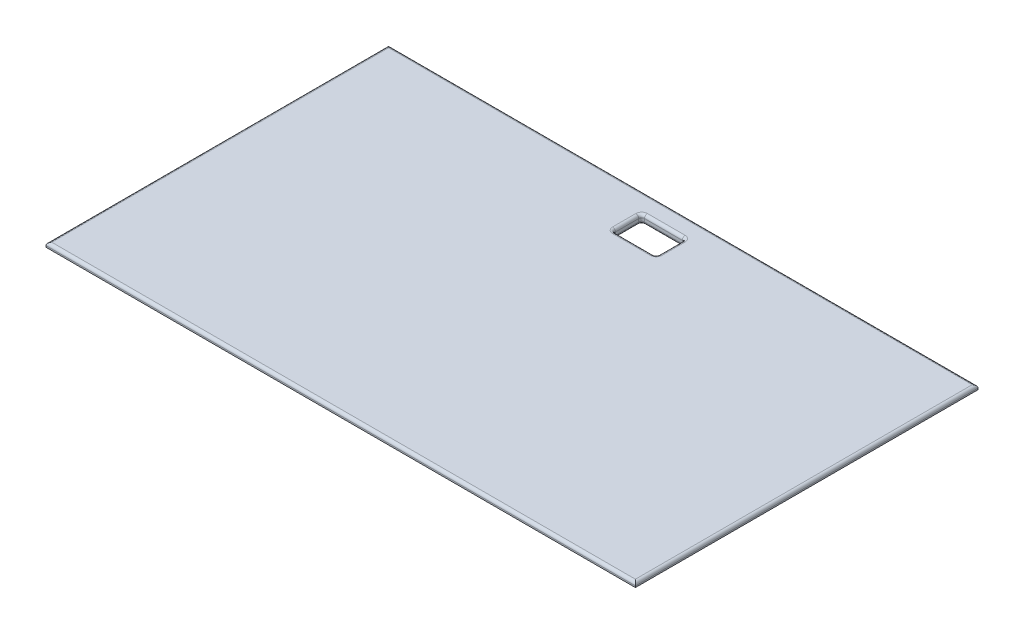
SolidWorks part; units mm, degrees
ref_plane "前视基准面" through (0, 0, 0) normal (0, 0, 1) x (1, 0, 0)
ref_plane "上视基准面" through (0, 0, 0) normal (0, 1, 0) x (1, 0, 0)
ref_plane "右视基准面" through (0, 0, 0) normal (1, 0, 0) x (0, 0, -1)
other "Configuration Table"
sketch "草图1" plane through (0, 0, 0) normal (0, 1, 0) x (1, 0, 0)
  line L1 (-100, -57.5) -> (100, -57.5)
  line L2 (-100, -57.5) -> (-100, 57.5)
  line L3 (-100, 57.5) -> (100, 57.5)
  line L4 (100, -57.5) -> (100, 57.5)
  line L5 (-100, -57.5) -> (100, 57.5) construction
  line L6 (-100, 57.5) -> (100, -57.5) construction
  point P0 (0, 0)
  dimension "D1" = 115
  dimension "D2" = 200
extrude "凸台-拉伸1" add sketch "草图1" along normal blind 1.5
ref_plane "基准面1" through (0, 1.5, 0) normal (0, 1, 0) x (1, 0, 0)
sketch "草图2" plane through (0, 1.5, 0) normal (0, 1, 0) x (1, 0, 0)
  line L0 (100, -57.5) -> (100, 57.5) construction
  line L1 (100, 57.5) -> (-100, 57.5) construction
  line L2 (100, -57.5) -> (100, 57.5) construction
  line L3 (100, 57.5) -> (-100, 57.5) construction
  line L21 (-101.5, -59) -> (101.5, -59)
  line L22 (-101.5, -59) -> (-101.5, 59)
  line L23 (-101.5, 59) -> (101.5, 59)
  line L24 (101.5, -59) -> (101.5, 59)
  line L25 (-101.5, -59) -> (101.5, 59) construction
  line L26 (-101.5, 59) -> (101.5, -59) construction
  point P2 (0, 0)
  dimension "D1" = 1.5
  dimension "D2" = 1.5
extrude "凸台-拉伸2" add sketch "草图2" along normal blind 1.5
sketch "草图3" plane through (0, 0, 0) normal (0, -1, 0) x (1, 0, 0)
  line L0 (0, 0) -> (0, -57.5) construction
  line L1 (100, -57.5) -> (-100, -57.5) construction
  line L3 (-7.5, -42.148) -> (7.5, -42.148)
  line L4 (-7.5, -42.148) -> (-7.5, -52.148)
  line L5 (-7.5, -52.148) -> (7.5, -52.148)
  line L6 (7.5, -42.148) -> (7.5, -52.148)
  line L7 (-7.5, -42.148) -> (7.5, -52.148) construction
  line L8 (-7.5, -52.148) -> (7.5, -42.148) construction
  point P5 (0, -47.148)
  dimension "D1" = 10
  dimension "D2" = 15
extrude "切除-拉伸1" cut sketch "草图3" against normal blind 11.5
fillet "圆角2" radius 1 12 edges at (7.5, 0, -47.148) (0, 0, -52.148) (0, 0, -42.148) (-7.5, 0, -47.148) (0, 3, -52.148) (7.5, 3, -47.148) (0, 3, -42.148) (-7.5, 3, -47.148) (-7.5, 1.5, -52.148) (7.5, 1.5, -52.148) (-7.5, 1.5, -42.148) (7.5, 1.5, -42.148)
fillet "圆角3" radius 1 4 edges at (0, 3, 59) (-101.5, 3, 0) (0, 3, -59) (101.5, 3, 0)
sketch "草图4" plane through (0, 0, 0) normal (0, -1, 0) x (1, 0, 0)
  line L0 (0, 57.5) -> (0, -57.5) construction
  line L1 (-100, 57.5) -> (100, 57.5) construction
  line L2 (100, -57.5) -> (-100, -57.5) construction
  line L3 (-100, 29.0019) -> (100, 29.0019) construction
  line L4 (26.25, -1.494) -> (-26.25, -1.494) construction
  line L5 (26.25, -1.494) -> (26.25, -30.294) construction
  line L6 (26.25, -30.294) -> (-26.25, -30.294) construction
  line L7 (-26.25, -1.494) -> (-26.25, -30.294) construction
  line L8 (26.25, -1.494) -> (-26.25, -30.294) construction
  line L9 (26.25, -30.294) -> (-26.25, -1.494) construction
  line L10 (-100, -57.5) -> (-100, 57.5) construction
  line L11 (100, 57.5) -> (100, -57.5) construction
  line L12 (-64.6953, 41.0019) -> (-64.6953, 42.5019)
  line L13 (-27.1953, 17.0019) -> (-69.6953, 17.0019) construction
  line L14 (-27.1953, 17.0019) -> (-27.1953, 41.0019) construction
  line L15 (-27.1953, 41.0019) -> (-69.6953, 41.0019) construction
  line L16 (-69.6953, 17.0019) -> (-69.6953, 41.0019) construction
  line L17 (-27.1953, 17.0019) -> (-69.6953, 41.0019) construction
  line L18 (-27.1953, 41.0019) -> (-69.6953, 17.0019) construction
  line L19 (25.3357, 14.2519) -> (78.8357, 14.2519) construction
  line L20 (25.3357, 14.2519) -> (25.3357, 43.7519) construction
  line L21 (25.3357, 43.7519) -> (78.8357, 43.7519) construction
  line L22 (78.8357, 14.2519) -> (78.8357, 43.7519) construction
  line L23 (25.3357, 14.2519) -> (78.8357, 43.7519) construction
  line L24 (25.3357, 43.7519) -> (78.8357, 14.2519) construction
  line L25 (-64.6953, 42.5019) -> (-71.1953, 42.5019)
  line L26 (-71.1953, 42.5019) -> (-71.1953, 36.0019)
  line L27 (-71.1953, 36.0019) -> (-69.6953, 36.0019)
  line L28 (-69.6953, 36.0019) -> (-69.6953, 41.0019)
  line L29 (-69.6953, 41.0019) -> (-64.6953, 41.0019)
  line L36 (-21.25, -1.494) -> (-21.25, 0.006)
  line L37 (-21.25, 0.006) -> (-27.75, 0.006)
  line L38 (-27.75, 0.006) -> (-27.75, -6.494)
  line L39 (-27.75, -6.494) -> (-26.25, -6.494)
  line L40 (-26.25, -6.494) -> (-26.25, -1.494)
  line L41 (-26.25, -1.494) -> (-21.25, -1.494)
  line L42 (-48.4453, 41.0019) -> (-48.4453, 17.0019) construction
  line L43 (52.0857, 43.7519) -> (52.0857, 14.2519) construction
  line L44 (-32.1953, 41.0019) -> (-32.1953, 42.5019)
  line L45 (-27.1953, 41.0019) -> (-32.1953, 41.0019)
  line L46 (-27.1953, 36.0019) -> (-27.1953, 41.0019)
  line L47 (-25.6953, 36.0019) -> (-27.1953, 36.0019)
  line L48 (-25.6953, 42.5019) -> (-25.6953, 36.0019)
  line L49 (-32.1953, 42.5019) -> (-25.6953, 42.5019)
  line L50 (-25.6953, 22.0019) -> (-27.1953, 22.0019)
  line L51 (-25.6953, 15.5019) -> (-25.6953, 22.0019)
  line L52 (-27.1953, 22.0019) -> (-27.1953, 17.0019)
  line L53 (-27.1953, 17.0019) -> (-32.1953, 17.0019)
  line L54 (-32.1953, 15.5019) -> (-25.6953, 15.5019)
  line L55 (-32.1953, 17.0019) -> (-32.1953, 15.5019)
  line L56 (-71.1953, 22.0019) -> (-69.6953, 22.0019)
  line L57 (-69.6953, 22.0019) -> (-69.6953, 17.0019)
  line L58 (-71.1953, 15.5019) -> (-71.1953, 22.0019)
  line L59 (-69.6953, 17.0019) -> (-64.6953, 17.0019)
  line L60 (-64.6953, 17.0019) -> (-64.6953, 15.5019)
  line L61 (-64.6953, 15.5019) -> (-71.1953, 15.5019)
  line L62 (27.75, -6.494) -> (26.25, -6.494)
  line L63 (21.25, -1.494) -> (21.25, 0.006)
  line L64 (26.25, -6.494) -> (26.25, -1.494)
  line L65 (26.25, -1.494) -> (21.25, -1.494)
  line L66 (21.25, 0.006) -> (27.75, 0.006)
  line L67 (27.75, 0.006) -> (27.75, -6.494)
  line L68 (-26.25, -15.894) -> (26.25, -15.894) construction
  line L69 (-26.25, -30.294) -> (-21.25, -30.294)
  line L70 (21.25, -30.294) -> (21.25, -31.794)
  line L71 (27.75, -25.294) -> (26.25, -25.294)
  line L72 (26.25, -25.294) -> (26.25, -30.294)
  line L73 (27.75, -31.794) -> (27.75, -25.294)
  line L74 (26.25, -30.294) -> (21.25, -30.294)
  line L75 (21.25, -31.794) -> (27.75, -31.794)
  line L76 (-27.75, -25.294) -> (-26.25, -25.294)
  line L77 (-21.25, -30.294) -> (-21.25, -31.794)
  line L78 (-26.25, -25.294) -> (-26.25, -30.294)
  line L79 (-27.75, -31.794) -> (-27.75, -25.294)
  line L80 (-21.25, -31.794) -> (-27.75, -31.794)
  line L81 (48.0857, 43.7519) -> (48.0857, 45.2519)
  line L82 (48.0857, 45.2519) -> (56.0857, 45.2519)
  line L83 (56.0857, 45.2519) -> (56.0857, 43.7519)
  line L84 (56.0857, 43.7519) -> (48.0857, 43.7519)
  line L85 (25.3357, 19.2519) -> (23.8357, 19.2519)
  line L86 (23.8357, 19.2519) -> (23.8357, 12.7519)
  line L87 (23.8357, 12.7519) -> (30.3357, 12.7519)
  line L88 (30.3357, 12.7519) -> (30.3357, 14.2519)
  line L89 (30.3357, 14.2519) -> (25.3357, 14.2519)
  line L90 (25.3357, 14.2519) -> (25.3357, 19.2519)
  line L91 (73.8357, 12.7519) -> (73.8357, 14.2519)
  line L92 (80.3357, 12.7519) -> (73.8357, 12.7519)
  line L93 (73.8357, 14.2519) -> (78.8357, 14.2519)
  line L94 (80.3357, 19.2519) -> (80.3357, 12.7519)
  line L95 (78.8357, 19.2519) -> (80.3357, 19.2519)
  line L96 (78.8357, 14.2519) -> (78.8357, 19.2519)
  point P6 (0, -15.894)
  point P11 (-48.4453, 29.0019)
  point P22 (52.0857, 29.0019)
  point P81 (52.0857, 43.7519)
  dimension "D1" = 28.8
  dimension "D2" = 52.5
  dimension "D3" = 42.5
  dimension "D4" = 24
  dimension "D5" = 53.5
  dimension "D6" = 29.5
  dimension "D7" = 1.5
  dimension "D8" = 1.5
  dimension "D9" = 5
  dimension "D10" = 5
  dimension "D11" = 1.5
  dimension "D12" = 1.5
  dimension "D13" = 5
  dimension "D14" = 5
  dimension "D15" = 1.5
  dimension "D16" = 1.5
  dimension "D17" = 5
  dimension "D18" = 5
  dimension "D19" = 1.5
  dimension "D20" = 8
extrude "凸台-拉伸3" add sketch "草图4" along normal blind 5
